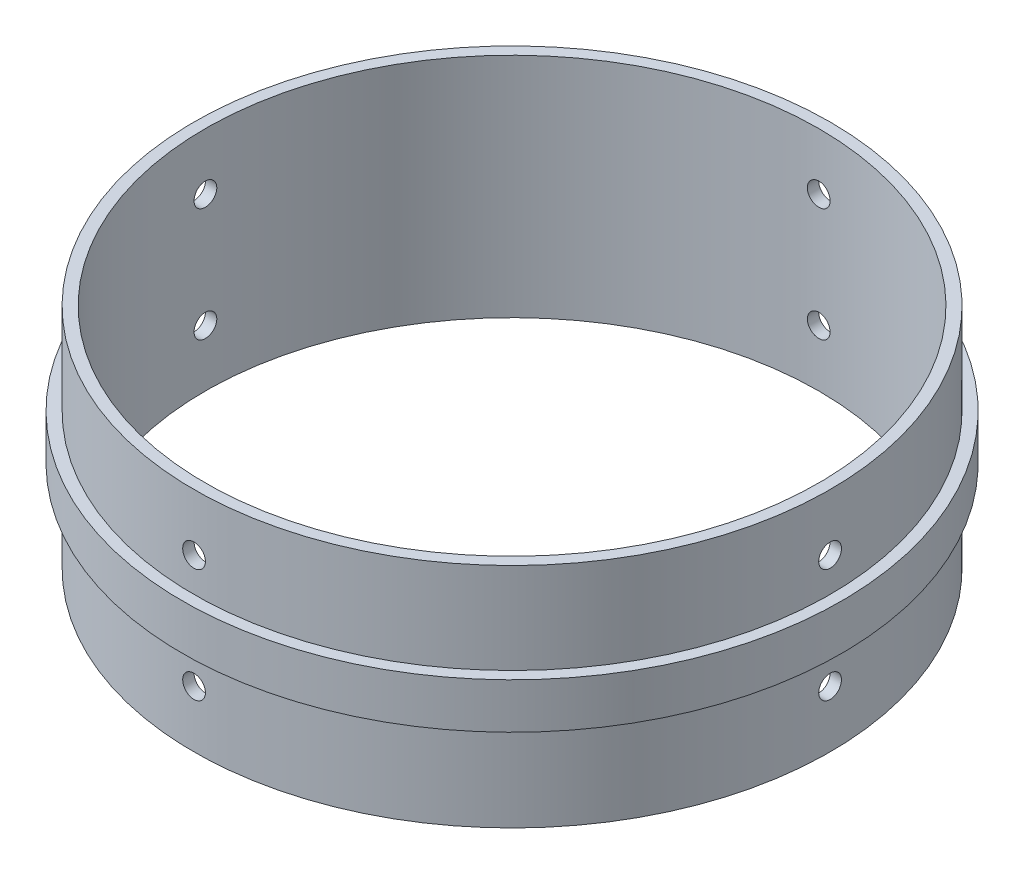
SolidWorks part; units mm, degrees
material "XStrand Filament"
ref_plane "Front Plane" through (0, 0, 0) normal (0, 0, 1) x (1, 0, 0)
ref_plane "Top Plane" through (0, 0, 0) normal (0, 1, 0) x (1, 0, 0)
ref_plane "Right Plane" through (0, 0, 0) normal (1, 0, 0) x (0, 0, -1)
sketch "Sketch1" plane through (0, 0, 0) normal (0, 0, 1) x (1, 0, 0)
  line L0 (0, 0) -> (0, 63.5) construction
  line L1 (92.075, 25.4) -> (92.075, 38.1)
  line L2 (85.725, 0) -> (85.725, 63.5)
  line L3 (92.075, 31.75) -> (85.725, 31.75) construction
  line L6 (92.075, 38.1) -> (88.9, 38.1)
  line L7 (88.9, 63.5) -> (88.9, 38.1)
  line L8 (88.9, 63.5) -> (85.725, 63.5)
  line L9 (92.075, 0) -> (92.075, 63.5) construction
  line L10 (92.075, 25.4) -> (88.9, 25.4)
  line L11 (88.9, 0) -> (88.9, 25.4)
  line L12 (88.9, 0) -> (85.725, 0)
  dimension "D1" = 63.5
  dimension "D4" = 25.4
  dimension "D5" = 88.9
  dimension "D2" = 92.075
  dimension "D3" = 6.35
revolve "Revolve1" add sketch "Sketch1" angle 360 about L0
sketch "Sketch2" plane through (0, 0, 0) normal (0, 0, 1) x (1, 0, 0)
  line L0 (0, 0) -> (0, 31.75) construction
  line L2 (0, 31.75) -> (0, 63.5) construction
  line L3 (88.9, 63.5) -> (-88.9, 63.5) construction
  circle A0 centre (0, 47.625) radius 3.175
  circle A1 centre (0, 15.875) radius 3.175
  point P5 (0, 31.75)
  dimension "D1" = 6.35
extrude "Cut-Extrude1" cut sketch "Sketch2" against normal through all both and the other way through all
sketch "Sketch3" plane through (0, 0, 0) normal (1, 0, 0) x (0, 0, -1)
  line L0 (0, 0) -> (0, 31.75) construction
  line L1 (0, 31.75) -> (0, 63.5) construction
  line L2 (85.725, 63.5) -> (-85.725, 63.5) construction
  circle A0 centre (0, 47.625) radius 3.175
  circle A1 centre (0, 15.875) radius 3.175
  point P4 (0, 31.75)
  point P8 (0, 0)
  point P10 (0, 0)
  point P11 (0, 63.5)
  point P14 (0, 0)
  point P15 (0, 0)
  dimension "D1" = 6.35
extrude "Cut-Extrude2" cut sketch "Sketch3" against normal through all both and the other way through all
